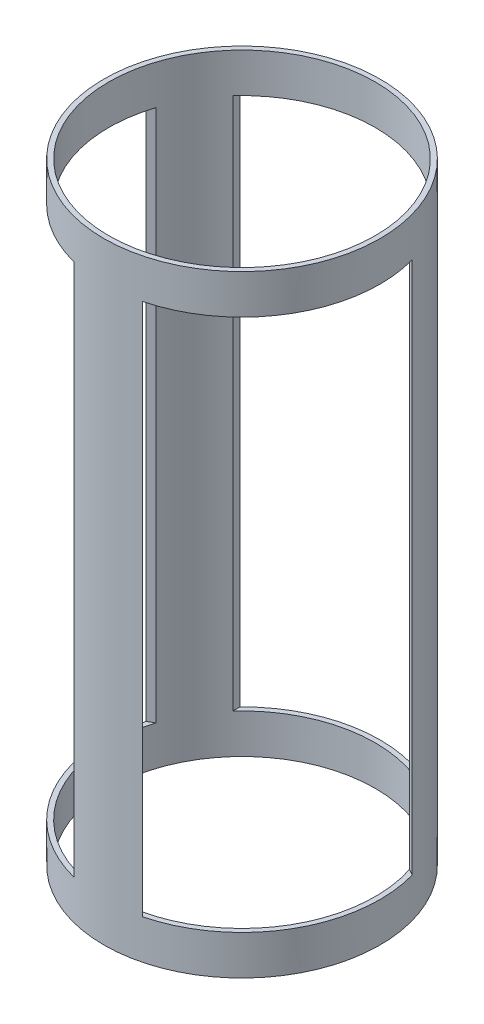
SolidWorks part; units mm, degrees
material "6061-T6 (SS)"
ref_plane "Front Plane" through (0, 0, 0) normal (0, 0, 1) x (1, 0, 0)
ref_plane "Top Plane" through (0, 0, 0) normal (0, 1, 0) x (1, 0, 0)
ref_plane "Right Plane" through (0, 0, 0) normal (1, 0, 0) x (0, 0, -1)
sketch "Sketch1" plane through (0, 0, 0) normal (0, 1, 0) x (1, 0, 0)
  circle A0 centre (0, 0) radius 88.9
  circle A1 centre (0, 0) radius 85.725
  dimension "D1" = 177.8
  dimension "D2" = 171.45
extrude "Boss-Extrude1" add sketch "Sketch1" along normal mid plane 393.7
sketch "Sketch2" plane through (0, 0, 0) normal (0, 0, 1) x (1, 0, 0)
  line L0 (85.725, 196.85) -> (-85.725, 196.85) construction
  line L1 (-63.5, -171.45) -> (63.5, -171.45)
  line L2 (-63.5, -171.45) -> (-63.5, 171.45)
  line L3 (-63.5, 171.45) -> (63.5, 171.45)
  line L4 (63.5, -171.45) -> (63.5, 171.45)
  line L5 (-63.5, -171.45) -> (63.5, 171.45) construction
  line L6 (-63.5, 171.45) -> (63.5, -171.45) construction
  line L7 (88.9, -196.85) -> (88.9, 196.85) construction
  point P0 (0, 0)
  dimension "D1" = 25.4
  dimension "D2" = 25.4
extrude "Cut-Extrude1" cut sketch "Sketch2" against normal up to surface (62.217 mm away)
pattern_circular "CirPattern1" count 3 over 360 about axis through (0, 0, 0) along (0, 1, 0) of "Cut-Extrude1"
